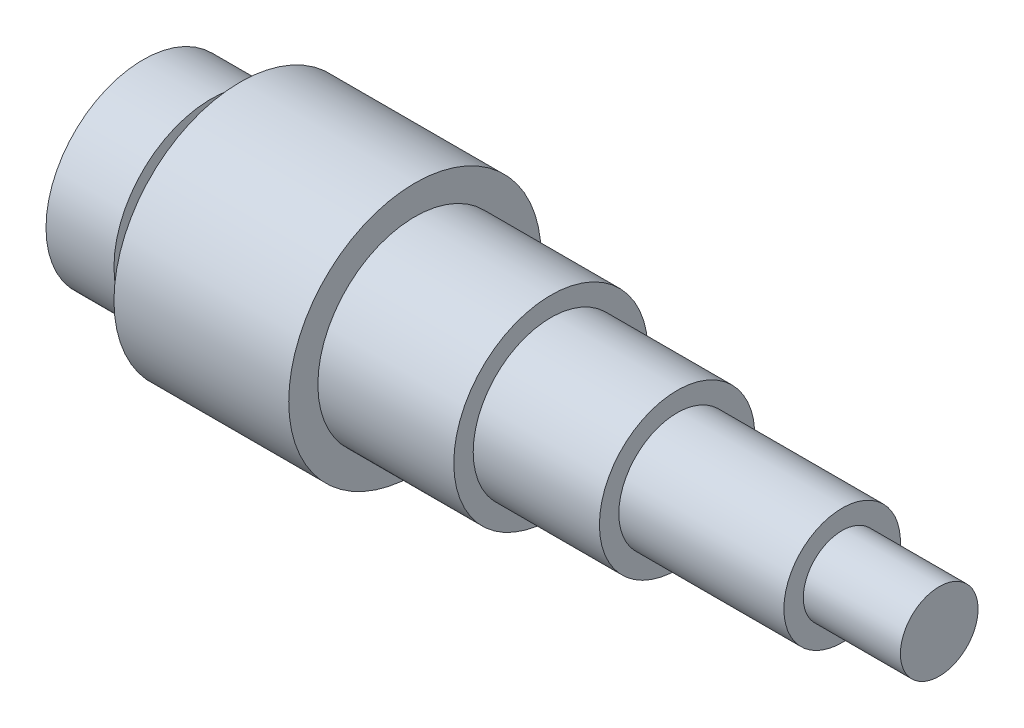
SolidWorks part; units mm, degrees
ref_plane "Front Plane" through (0, 0, 0) normal (0, 0, 1) x (1, 0, 0)
ref_plane "Top Plane" through (0, 0, 0) normal (0, 1, 0) x (1, 0, 0)
ref_plane "Right Plane" through (0, 0, 0) normal (1, 0, 0) x (0, 0, -1)
sketch "Sketch1" plane through (0, 0, 0) normal (0, 1, 0) x (1, 0, 0)
  line L0 (0, 0) -> (72.9, 0) construction
  line L1 (-3.5, 0) -> (78.5, 0)
  line L3 (-3.5, 0) -> (-3.5, -10)
  line L4 (-3.5, -10) -> (3.5, -10)
  line L6 (0, 0) -> (3.5, -10) construction
  line L7 (-3.5, -10) -> (0, 0) construction
  line L13 (3.5, 0) -> (3.5, -8)
  line L14 (3.5, -8) -> (6.5, -8)
  line L15 (6.5, 0) -> (6.5, -8)
  line L18 (6.5, -13) -> (24.5, -13)
  line L21 (24.5, 0) -> (24.5, -10)
  line L22 (24.5, -10) -> (38.5, -10)
  line L25 (38.5, 0) -> (38.5, -8)
  line L26 (38.5, -8) -> (51.5, -8)
  line L29 (51.5, 0) -> (51.5, -6)
  line L30 (51.5, -6) -> (68.5, -6)
  line L32 (68.5, -4) -> (78.5, -4)
  line L33 (68.5, -4) -> (68.5, 0)
  line L35 (78.5, -4) -> (78.5, 0)
  line L36 (68.5, 0) -> (68.5, -6)
  line L37 (51.5, 0) -> (51.5, -8)
  line L38 (38.5, 0) -> (38.5, -10)
  line L39 (24.5, 0) -> (24.5, -13)
  line L40 (6.5, 0) -> (6.5, -13)
  line L41 (3.5, 0) -> (3.5, -10)
  dimension "D1" = 7
  dimension "D3" = 10
  dimension "D8" = 82
revolve "Revolve2" add sketch "Sketch1" angle 360 about L1
sketch "Sketch2" plane through (-3.5, 0, 0) normal (-1, 0, 0) x (0, 0, 1)
  circle A0 centre (0, 0) radius 2.5
  dimension "D1" = 5
extrude "Cut-Extrude1" cut sketch "Sketch2" against normal blind 36
sketch "Sketch3" plane through (0, 0, 0) normal (0, 0, 1) x (1, 0, 0)
  line L0 (34.5, 0) -> (28.5789, 0) construction
  line L3 (32.5, -2.5) -> (34.5, -2.5) construction
  line L6 (34.5, -2.5) -> (34.5, 0) construction
  line L7 (32.5, -2.5) -> (34.5, 0)
  line L8 (34.5, -2.5) -> (34.5, 0) construction
  line L9 (34.5, 0) -> (32.5, -2.5)
  line L10 (-3.5, 10) -> (-3.5, -10) construction
  line L11 (32.5, -2.5) -> (32.5, 0)
  line L12 (32.5, 0) -> (34.5, 0)
  dimension "D1" = 2.5
  dimension "D2" = 2
  dimension "D3" = 38
revolve "Cut-Revolve2" cut sketch "Sketch3" angle 360 about L0
